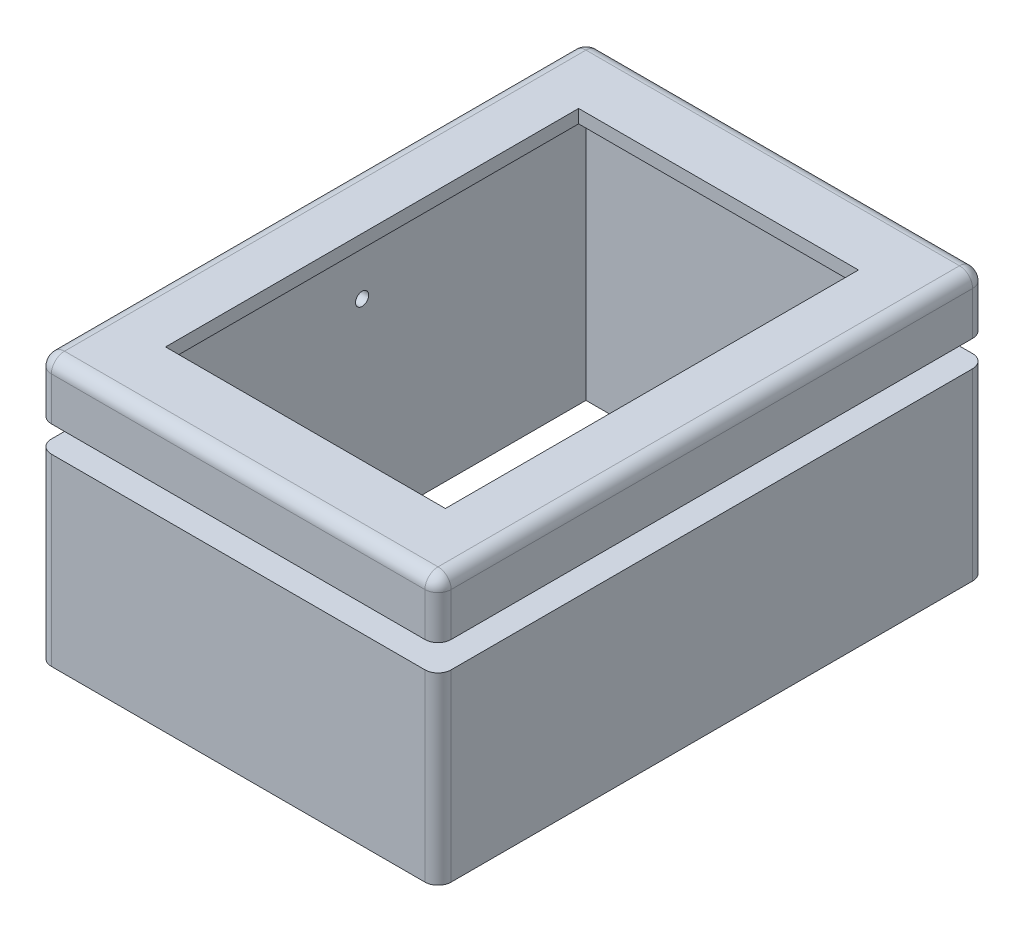
SolidWorks part; units mm, degrees
material "ABS"
ref_plane "Front Plane" through (0, 0, 0) normal (0, 0, 1) x (1, 0, 0)
ref_plane "Top Plane" through (0, 0, 0) normal (0, 1, 0) x (1, 0, 0)
ref_plane "Right Plane" through (0, 0, 0) normal (1, 0, 0) x (0, 0, -1)
sketch "Sketch1" plane through (0, 0, 0) normal (0, 1, 0) x (1, 0, 0)
  line L0 (12.954, 10.4394) -> (15.24, 10.4394) construction
  line L1 (0, 0) -> (15.24, 0)
  line L2 (0, 0) -> (0, 20.8788)
  line L3 (0, 20.8788) -> (15.24, 20.8788)
  line L4 (15.24, 0) -> (15.24, 20.8788)
  line L5 (2.286, 18.3134) -> (12.954, 18.3134)
  line L6 (2.286, 18.3134) -> (2.286, 2.5654)
  line L7 (2.286, 2.5654) -> (12.954, 2.5654)
  line L8 (12.954, 18.3134) -> (12.954, 2.5654)
  line L9 (7.62, 18.3134) -> (7.62, 20.8788) construction
  dimension "D1" = 15.24
  dimension "D2" = 20.8788
  dimension "D3" = 15.748
  dimension "D4" = 10.668
extrude "Boss-Extrude1" add sketch "Sketch1" along normal blind 10.16
sketch "Sketch2" plane through (15.24, 0, 0) normal (1, 0, 0) x (0, 0, -1)
  line L0 (10.4394, 7.62) -> (10.4394, 10.16) construction
  line L1 (0, 10.16) -> (20.8788, 10.16) construction
  circle A0 centre (10.4394, 7.62) radius 0.25
  dimension "D1" = 0.5
  dimension "D2" = 2.54
extrude "Cut-Extrude1" cut sketch "Sketch2" against normal through all
sketch "Sketch3" plane through (0, 0, 0) normal (0, -1, 0) x (1, 0, 0)
  line L8 (1.905, -1.905) -> (1.905, -18.9738)
  line L9 (1.905, -18.9738) -> (13.335, -18.9738)
  line L10 (13.335, -18.9738) -> (13.335, -1.905)
  line L11 (13.335, -1.905) -> (1.905, -1.905)
  line L12 (1.905, -1.905) -> (1.905, -18.9738)
  line L13 (1.905, -18.9738) -> (13.335, -18.9738)
  line L14 (13.335, -18.9738) -> (13.335, -1.905)
  line L15 (13.335, -1.905) -> (1.905, -1.905)
  dimension "D1" = 1.905
extrude "Cut-Extrude2" cut sketch "Sketch3" against normal offset from surface (9.652 mm away) 0.508 up to face at (7.62, 10.16, -10.4394)
ref_plane "Plane2" through (0, 8.01, 0) normal (0, 1, 0) x (1, 0, 0)
sketch "Sketch5" plane through (0, 8.01, 0) normal (0, 1, 0) x (1, 0, 0)
  line L0 (15.24, 20.8788) -> (15.24, 0)
  line L1 (15.24, 20.8788) -> (15.24, 0)
  line L2 (0, 20.8788) -> (15.24, 20.8788)
  line L3 (0, 20.8788) -> (15.24, 20.8788)
  line L4 (0, 0) -> (0, 20.8788)
  line L5 (0, 0) -> (0, 20.8788)
  line L6 (15.24, 0) -> (0, 0)
  line L7 (15.24, 0) -> (0, 0)
  line L8 (13.74, 19.3788) -> (13.74, 1.5)
  line L9 (13.74, 1.5) -> (1.5, 1.5)
  line L10 (1.5, 1.5) -> (1.5, 19.3788)
  line L11 (1.5, 19.3788) -> (13.74, 19.3788)
  dimension "D1" = 1.5
extrude "Cut-Extrude4" cut sketch "Sketch5" against normal blind 1
fillet "Fillet1" radius 0.5 12 edges at (15.24, 3.505, -20.8788) (15.24, 9.085, -20.8788) (7.62, 10.16, -20.8788) (0, 3.505, -20.8788) (0, 9.085, -20.8788) (0, 10.16, -10.4394) (0, 9.085, 0) (0, 3.505, 0) (15.24, 3.505, 0) (15.24, 9.085, 0) (7.62, 10.16, 0) (15.24, 10.16, -10.4394)
